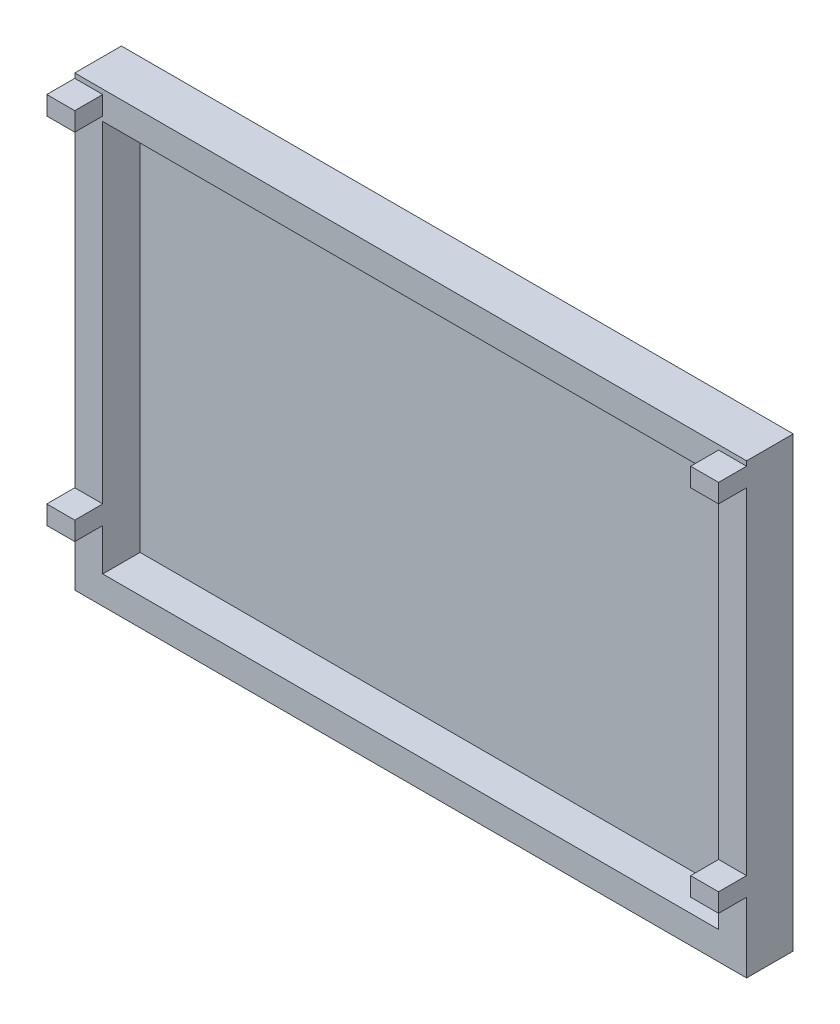
SolidWorks part; units mm, degrees
ref_plane "Front Plane" through (0, 0, 0) normal (0, 0, 1) x (1, 0, 0)
ref_plane "Top Plane" through (0, 0, 0) normal (0, 1, 0) x (1, 0, 0)
ref_plane "Right Plane" through (0, 0, 0) normal (1, 0, 0) x (0, 0, -1)
sketch "Sketch1" plane through (0, 0, 0) normal (0, 0, 1) x (1, 0, 0)
  line L1 (0, 0) -> (1828.8, 0)
  line L2 (0, 0) -> (0, 1219.2)
  line L3 (0, 1219.2) -> (1828.8, 1219.2)
  line L4 (1828.8, 0) -> (1828.8, 1219.2)
  dimension "D1" = 1219.2
  dimension "D2" = 1828.8
extrude "Boss-Extrude1" add sketch "Sketch1" along normal blind 127 contours L2 L3 L4 L1
sketch "Sketch2" plane through (0, 0, 127) normal (0, 0, 1) x (1, 0, 0)
  line L0 (1828.8, 0) -> (1828.8, 1219.2) construction
  line L1 (1752.6, 1143) -> (76.2, 1143)
  line L2 (1752.6, 1143) -> (1752.6, 76.2)
  line L3 (1752.6, 76.2) -> (76.2, 76.2)
  line L4 (76.2, 1143) -> (76.2, 76.2)
  line L5 (0, 1219.2) -> (1828.8, 1219.2) construction
  line L6 (0, 0) -> (0, 1219.2) construction
  line L7 (0, 0) -> (1828.8, 0) construction
  dimension "D1" = 76.2
  dimension "D2" = 76.2
  dimension "D3" = 76.2
  dimension "D4" = 76.2
extrude "Cut-Extrude2" cut sketch "Sketch2" against normal blind 101.6
sketch "Sketch3" plane through (0, 0, 127) normal (0, 0, 1) x (1, 0, 0)
  line L0 (0, 1219.2) -> (1828.8, 1219.2) construction
  line L1 (0, 1206.5) -> (76.2, 1206.5)
  line L2 (0, 1206.5) -> (0, 1155.7)
  line L3 (0, 1155.7) -> (76.2, 1155.7)
  line L4 (76.2, 1206.5) -> (76.2, 1155.7)
  line L5 (0, 0) -> (0, 1219.2) construction
  dimension "D1" = 76.2
  dimension "D2" = 50.8
  dimension "D3" = 12.7
extrude "Boss-Extrude2" add sketch "Sketch3" along normal blind 76.2
sketch "Sketch4" plane through (0, 0, 127) normal (0, 0, 1) x (1, 0, 0)
  line L0 (1828.8, 0) -> (1828.8, 1219.2) construction
  line L1 (1752.6, 1206.5) -> (1828.8, 1206.5)
  line L2 (1752.6, 1206.5) -> (1752.6, 1155.7)
  line L3 (1752.6, 1155.7) -> (1828.8, 1155.7)
  line L4 (1828.8, 1206.5) -> (1828.8, 1155.7)
  line L5 (0, 1219.2) -> (1828.8, 1219.2) construction
  dimension "D1" = 12.7
  dimension "D2" = 76.2
  dimension "D3" = 50.8
extrude "Boss-Extrude3" add sketch "Sketch4" along normal blind 76.2
sketch "Sketch5" plane through (0, 0, 127) normal (0, 0, 1) x (1, 0, 0)
  line L0 (0, 0) -> (0, 1155.7) construction
  line L1 (0, 241.3) -> (76.2, 241.3)
  line L2 (0, 241.3) -> (0, 190.5)
  line L3 (0, 190.5) -> (76.2, 190.5)
  line L4 (76.2, 241.3) -> (76.2, 190.5)
  line L5 (76.2, 1143) -> (76.2, 76.2) construction
  line L6 (1752.6, 76.2) -> (1752.6, 1143) construction
  line L7 (1752.6, 241.3) -> (1828.8, 241.3)
  line L8 (1752.6, 241.3) -> (1752.6, 190.5)
  line L9 (1752.6, 190.5) -> (1828.8, 190.5)
  line L10 (1828.8, 241.3) -> (1828.8, 190.5)
  line L11 (1828.8, 0) -> (1828.8, 1155.7) construction
  line L12 (0, 0) -> (1828.8, 0) construction
  dimension "D1" = 76.2
  dimension "D2" = 50.8
  dimension "D3" = 190.5
  dimension "D4" = 190.5
  dimension "D5" = 76.2
  dimension "D6" = 50.8
extrude "Boss-Extrude4" add sketch "Sketch5" along normal blind 76.2
